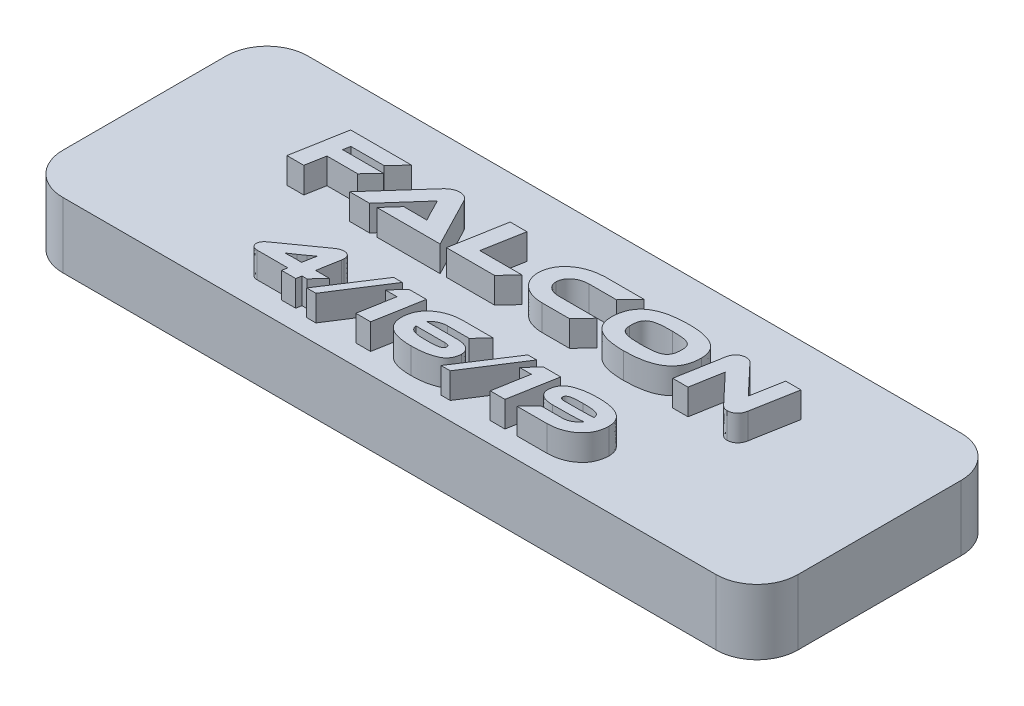
SolidWorks part; units mm, degrees
ref_plane "Front Plane" through (0, 0, 0) normal (0, 0, 1) x (1, 0, 0)
ref_plane "Top Plane" through (0, 0, 0) normal (0, 1, 0) x (1, 0, 0)
ref_plane "Right Plane" through (0, 0, 0) normal (1, 0, 0) x (0, 0, -1)
sketch "Sketch1" plane through (0, 0, 0) normal (0, 1, 0) x (1, 0, 0)
  line L1 (-28.575, 9.525) -> (28.575, 9.525)
  line L2 (-28.575, 9.525) -> (-28.575, -9.525)
  line L3 (-28.575, -9.525) -> (28.575, -9.525)
  line L4 (28.575, 9.525) -> (28.575, -9.525)
  line L5 (-28.575, 9.525) -> (28.575, -9.525) construction
  line L6 (-28.575, -9.525) -> (28.575, 9.525) construction
  point P0 (0, 0)
  dimension "D1" = 57.15
  dimension "D2" = 19.05
extrude "Boss-Extrude1" add sketch "Sketch1" along normal up to surface (5.08 mm away)
fillet "Fillet1" radius 3.175 4 edges at (-28.575, 2.54, 9.525) (-28.575, 2.54, -9.525) (28.575, 2.54, 9.525) (28.575, 2.54, -9.525)
sketch "Sketch3" plane through (0, 5.08, 0) normal (0, 1, 0) x (1, 0, 0)
  line L0 (28.575, -7.9375) -> (-28.575, -7.9375) construction
  line L1 (28.575, -6.35) -> (28.575, 6.35) construction
  line L2 (-28.575, 6.35) -> (-28.575, -6.35) construction
  line L3 (28.575, 0) -> (-28.575, 0) construction
  line L5 (-25.4, -9.525) -> (25.4, -9.525) construction
  line L6 (25.4, 9.525) -> (-25.4, 9.525) construction
  text T0 "Falcon" font "Ethnocentric Rg" height in points 16
  text T1 "4/16/19" font "Ethnocentric Rg" height in points 14
  point P8 (-28.575, 0)
  dimension "D1" = 1.5875
extrude "Boss-Extrude2" add sketch "Sketch3" along normal blind 2
sketch "Sketch4" plane through (0, 0, 0) normal (0, -1, 0) x (1, 0, 0)
  line L0 (25.4, 0) -> (-25.4, 0) construction
  circle A0 centre (-25.4, 0) radius 0.9
  circle A1 centre (25.4, 0) radius 0.9
  point P3 (0, 0)
  dimension "D2" = 1.8
  dimension "D1" = 50.8
extrude "Cut-Extrude1" cut sketch "Sketch4" against normal blind 4
